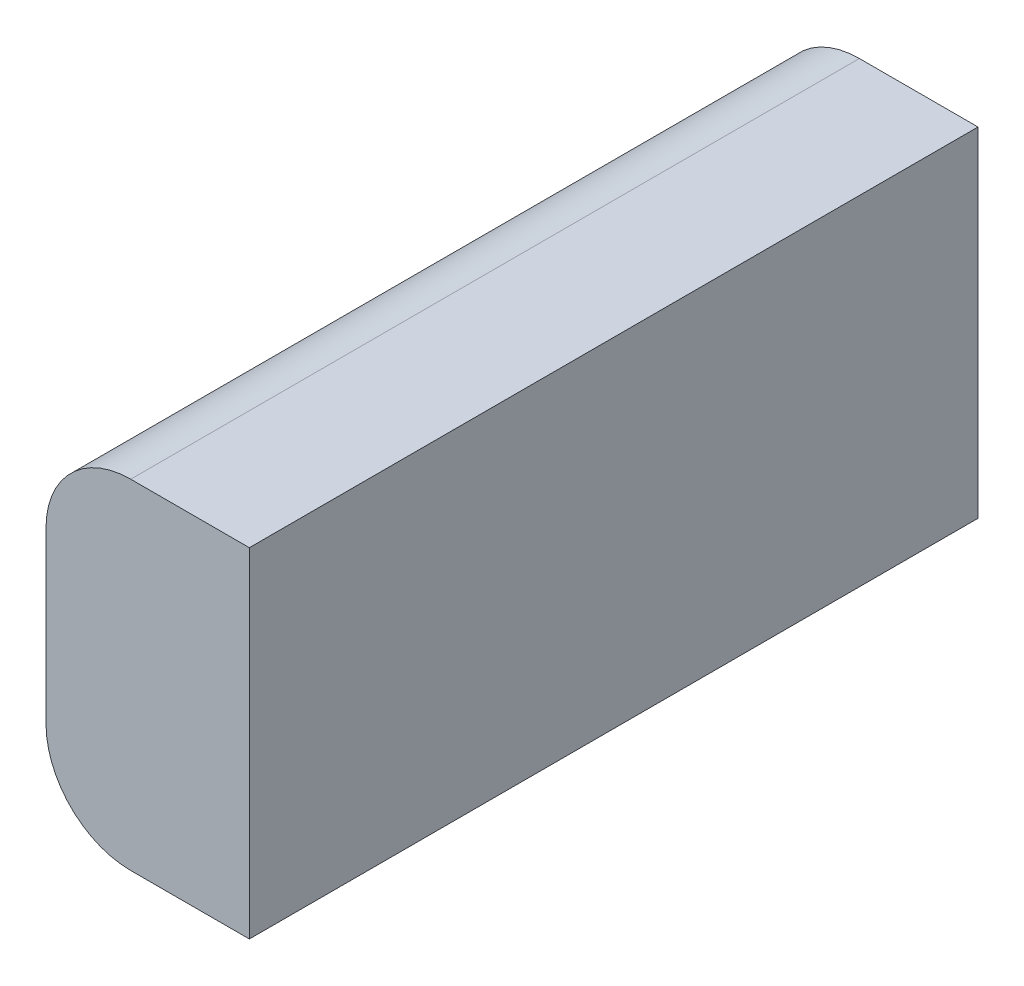
SolidWorks part; units mm, degrees
ref_plane "Front Plane" through (0, 0, 0) normal (0, 0, 1) x (1, 0, 0)
ref_plane "Top Plane" through (0, 0, 0) normal (0, 1, 0) x (1, 0, 0)
ref_plane "Right Plane" through (0, 0, 0) normal (1, 0, 0) x (0, 0, -1)
sketch "Sketch1" plane through (0, 0, 0) normal (0, 0, 1) x (1, 0, 0)
  line L1 (-2.5201, 111.0468) -> (73.6799, 111.0468)
  line L2 (-2.5201, 111.0468) -> (-2.5201, -15.9532)
  line L3 (-2.5201, -15.9532) -> (73.6799, -15.9532)
  line L4 (73.6799, 111.0468) -> (73.6799, -15.9532)
  dimension "D1" = 127
  dimension "D2" = 76.2
extrude "Boss-Extrude1" add sketch "Sketch1" along normal blind 273.05
fillet "Fillet1" radius 31.75 2 edges at (-2.5201, -15.9532, 136.525) (-2.5201, 111.0468, 136.525)
